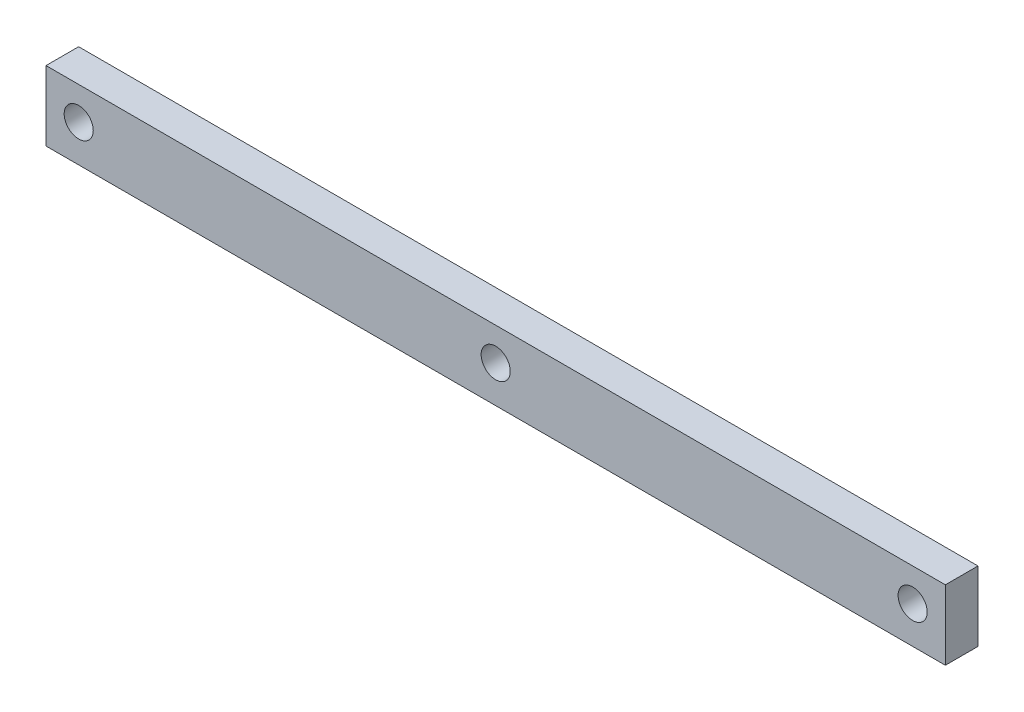
SolidWorks part; units mm, degrees
material "Maple"
ref_plane "Front Plane" through (0, 0, 0) normal (0, 0, 1) x (1, 0, 0)
ref_plane "Top Plane" through (0, 0, 0) normal (0, 1, 0) x (1, 0, 0)
ref_plane "Right Plane" through (0, 0, 0) normal (1, 0, 0) x (0, 0, -1)
sketch "Sketch1" plane through (0, 0, 0) normal (0, 0, 1) x (1, 0, 0)
  line L1 (-43.735, 4.85) -> (43.735, 4.85)
  line L2 (-43.735, 4.85) -> (-43.735, -4.85)
  line L3 (-43.735, -4.85) -> (43.735, -4.85)
  line L4 (43.735, 4.85) -> (43.735, -4.85)
  line L5 (-43.735, 4.85) -> (43.735, -4.85) construction
  line L6 (-43.735, -4.85) -> (43.735, 4.85) construction
  point P0 (0, 0)
  dimension "D1" = 87.47
  dimension "D2" = 9.7
extrude "Boss-Extrude1" add sketch "Sketch1" along normal blind 3.175
sketch "Sketch3" plane through (0, 0, 3.175) normal (0, 0, 1) x (1, 0, 0)
  line L0 (-43.735, 4.85) -> (-40.553, 1.668) construction
  line L1 (43.735, 4.85) -> (-43.735, 4.85) construction
  line L2 (0, 0) -> (0, 4.85) construction
  line L3 (-40.553, 1.668) -> (0, 1.668) construction
  circle A0 centre (-40.553, 1.668) radius 1.415
  circle A1 centre (0, 1.668) radius 1.415
  circle A2 centre (40.553, 1.668) radius 1.415
  dimension "D3" = 2.83
  dimension "D4" = 2.83
  dimension "D1" = 45
  dimension "D2" = 4.5
extrude "Cut-Extrude1" cut sketch "Sketch3" against normal blind 10
sketch "Sketch4" plane through (0, 0, 3.175) normal (0, 0, 1) x (1, 0, 0)
  line L0 (0, -4.85) -> (0, -1.93) construction
  line L1 (-43.735, -4.85) -> (43.735, -4.85) construction
  line L2 (0, -1.93) -> (-43.735, -1.93)
  line L3 (-43.735, 4.85) -> (-43.735, -4.85) construction
  line L4 (-43.735, -1.93) -> (-43.735, -4.85)
  line L5 (-43.735, -4.85) -> (43.735, -4.85)
  line L6 (43.735, -4.85) -> (43.735, -1.93)
  line L7 (43.735, -4.85) -> (43.735, 4.85) construction
  line L8 (43.735, -1.93) -> (0, -1.93)
  dimension "D1" = 2.92
extrude "Cut-Extrude2" cut sketch "Sketch4" against normal blind 10
equation "\"length\"=87.3"
equation "\"D1@Sketch1\"=\"length\" + 2*\"kerf\""
equation "\"width\"=9.7"
equation "\"D2@Sketch1\"=\"width\""
equation "\"depth\"=10"
equation "\"kerf\"= 0.17 / 2"
equation "\"D3@Sketch3\"= 3.00mm - 2*\"kerf\""
equation "\"D4@Sketch3\"= 3 - 2*\"kerf\""
